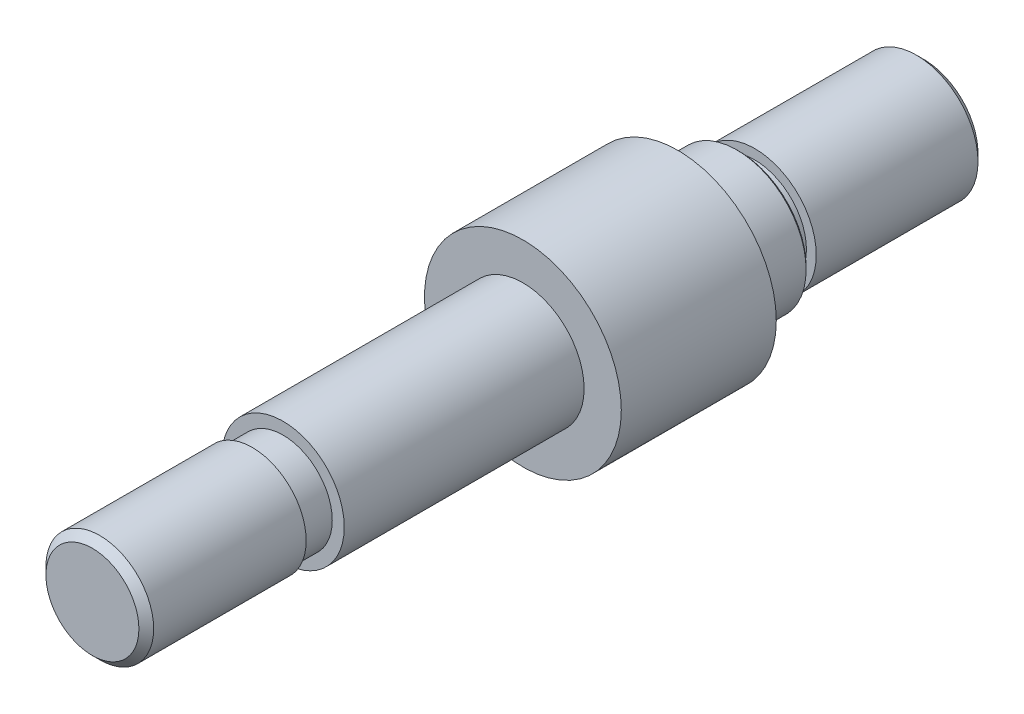
SolidWorks part; units mm, degrees
material "AISI 1020 Steel, Cold Rolled"
ref_plane "Front Plane" through (0, 0, 0) normal (0, 0, 1) x (1, 0, 0)
ref_plane "Top Plane" through (0, 0, 0) normal (0, 1, 0) x (1, 0, 0)
ref_plane "Right Plane" through (0, 0, 0) normal (1, 0, 0) x (0, 0, -1)
sketch "Sketch1" plane through (0, 0, 0) normal (0, 0, 1) x (1, 0, 0)
  circle A0 centre (0, 0) radius 7.1438
  dimension "D1" = 14.2875
extrude "Boss-Extrude1" add sketch "Sketch1" against normal blind 6.35
sketch "Sketch2" plane through (0, 0, 0) normal (0, 0, 1) x (1, 0, 0)
  circle A0 centre (0, 0) radius 10.16
  dimension "D1" = 20.32
extrude "Boss-Extrude2" add sketch "Sketch2" along normal blind 16.002
chamfer "Chamfer1" distance 0.254 angle 45 1 edges at (7.1438, 0, -6.35)
sketch "Sketch3" plane through (0, 0, 16.002) normal (0, 0, 1) x (1, 0, 0)
  circle A0 centre (0, 0) radius 6.3182
  dimension "D1" = 12.6365
extrude "Boss-Extrude3" add sketch "Sketch3" along normal blind 44.45
sketch "Sketch5" plane through (0, 0, -6.35) normal (0, 0, -1) x (-1, 0, 0)
  circle A0 centre (0, 0) radius 6.35
  dimension "D1" = 12.7
extrude "Boss-Extrude4" add sketch "Sketch5" along normal blind 19.05
cosmetic thread "Cosmetic Thread2" parameters "D1"=17.4625, "D2"=11.1887
sketch "Sketch11" plane through (0, 0, 60.452) normal (0, 0, 1) x (1, 0, 0)
  circle A0 centre (0, 0) radius 5.5626
  circle A1 centre (0, 0) radius 6.3183
  dimension "D1" = 11.1252
extrude "Cut-Extrude2" cut sketch "Sketch11" against normal blind 16.51
cosmetic thread "Cosmetic Thread3" parameters "D2"=9.6012
chamfer "Chamfer2" distance 0.762 angle 45 2 edges at (-6.35, 0, -25.4) (5.5626, 0, 60.452)
sketch "Sketch8" plane through (0, 0, 0) normal (0, 1, 0) x (1, 0, 0)
  line L0 (0, 0) -> (0, 44.4681) construction
  line L1 (0, 6.35) -> (-6.35, 6.35) construction
  line L2 (6.8897, 6.35) -> (-6.8897, 6.35) construction
  line L4 (-6.35, 6.35) -> (-5.334, 6.35)
  line L5 (-6.35, 6.35) -> (-6.35, 7.9375)
  line L6 (-6.35, 7.9375) -> (-5.334, 7.9375)
  line L7 (-5.334, 6.35) -> (-5.334, 7.9375)
  dimension "D1" = 6.35
  dimension "D2" = 1.016
  dimension "D3" = 1.5875
revolve "Cut-Revolve3" cut sketch "Sketch8" angle 360 about L0
sketch "Sketch10" plane through (0, 0, 0) normal (0, 1, 0) x (1, 0, 0)
  line L0 (0, -67.9849) -> (0, -27.7587) construction
  line L1 (0, -43.942) -> (-6.35, -43.942) construction
  line L3 (-4.8006, -60.452) -> (4.8006, -60.452) construction
  line L4 (-6.35, -43.942) -> (-5.08, -43.942)
  line L5 (-6.35, -43.942) -> (-6.35, -40.767)
  line L6 (-6.35, -40.767) -> (-5.08, -40.767)
  line L7 (-5.08, -43.942) -> (-5.08, -40.767)
  dimension "D1" = 16.51
  dimension "D2" = 6.35
  dimension "D3" = 1.27
  dimension "D4" = 3.175
revolve "Cut-Revolve4" cut sketch "Sketch10" angle 360 about L0
